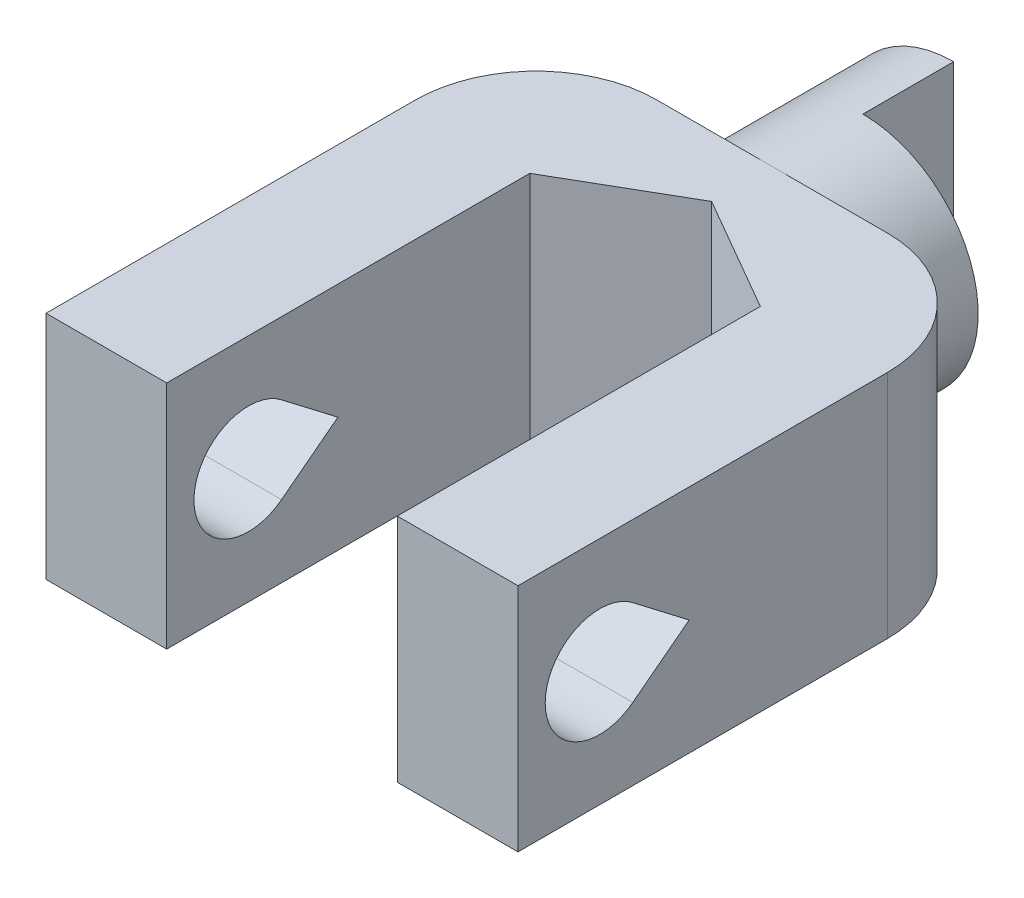
SolidWorks part; units mm, degrees
material "ABS"
ref_plane "Alzado" through (0, 0, 0) normal (0, 0, 1) x (1, 0, 0)
ref_plane "Planta" through (0, 0, 0) normal (0, 1, 0) x (1, 0, 0)
ref_plane "Vista lateral" through (0, 0, 0) normal (1, 0, 0) x (0, 0, -1)
sketch "Croquis1" plane through (0, 0, 0) normal (0, 0, 1) x (1, 0, 0)
  circle A0 centre (0, 0) radius 3.175
  dimension "D1" = 6.35
extrude "Saliente-Extruir1" add sketch "Croquis1" along normal blind 5
sketch "Croquis2" plane through (0, 0, 5) normal (0, 0, 1) x (1, 0, 0)
  line L1 (-6.5, -3.175) -> (6.5, -3.175)
  line L2 (-6.5, -3.175) -> (-6.5, 3.175)
  line L3 (-6.5, 3.175) -> (6.5, 3.175)
  line L4 (6.5, -3.175) -> (6.5, 3.175)
  line L5 (-6.5, -3.175) -> (6.5, 3.175) construction
  line L6 (-6.5, 3.175) -> (6.5, -3.175) construction
  point P0 (0, 0)
  dimension "D1" = 6.35
  dimension "D2" = 13
extrude "Saliente-Extruir2" add sketch "Croquis2" along normal blind 13.5
sketch "Croquis5" plane through (0, 0, 0) normal (0, 1, 0) x (1, 0, 0)
  line L0 (3.175, -5) -> (3.175, 0) construction
  line L1 (0, 0) -> (3.175, 0)
  line L2 (0, 0) -> (0, -2.5)
  line L3 (0, -2.5) -> (3.175, -2.5)
  line L4 (3.175, 0) -> (3.175, -2.5)
  dimension "D1" = 2.5
extrude "Cortar-Extruir2" cut sketch "Croquis5" against normal up to surface and the other way up to surface up to face at (0, 0, 5) other way up to face at (0, 0, 5)
sketch "Croquis7" plane through (0, 3.175, 0) normal (0, 1, 0) x (1, 0, 0)
  line L0 (-3.175, -18.5) -> (3.175, -18.5)
  line L1 (6.5, -18.5) -> (-6.5, -18.5) construction
  line L2 (-3.175, -18.5) -> (-3.175, -8.5)
  line L3 (-3.175, -8.5) -> (0, -6.6669)
  line L4 (0, -6.6669) -> (3.175, -8.5)
  line L5 (3.175, -8.5) -> (3.175, -18.5)
  point P5 (0, -18.5)
  dimension "D1" = 6.35
  dimension "D2" = 120
  dimension "D3" = 10
extrude "Cortar-Extruir6" cut sketch "Croquis7" against normal up to next
sketch "Croquis8" plane through (0, 3.175, 0) normal (0, 1, 0) x (1, 0, 0)
  line L0 (-6.5, -5) -> (-3.175, -5)
  line L1 (6.5, -5) -> (0, -5) construction
  line L2 (-3.175, 0) -> (-3.175, -5) construction
  line L4 (-6.5, -18.5) -> (-6.5, -5) construction
  line L5 (-6.5, -8.325) -> (-6.5, -5)
  arc A0 (-3.175, -5) -> (-6.5, -8.325) centre (-3.175, -8.325) ccw
extrude "Cortar-Extruir7" cut sketch "Croquis8" against normal up to next (6.35 mm away)
mirror "Simetría1" about plane through (0, 0, 0) normal (1, 0, 0) of "Cortar-Extruir7"
sketch "Croquis9" plane through (6.5, 0, 0) normal (1, 0, 0) x (0, 0, -1)
  line L0 (-18.5, -3.175) -> (-18.5, 3.175) construction
  line L1 (-15.3369, 1.19) -> (-13.786, 0)
  line L2 (-13.786, 0) -> (-15.3369, -1.19)
  arc A0 (-15.3369, 1.19) -> (-15.3369, -1.19) centre (-16.25, 0) ccw
  dimension "D1" = 3
  dimension "D2" = 2.25
  dimension "D3" = 75
extrude "Cortar-Extruir8" cut sketch "Croquis9" against normal up to surface (13 mm away) up to face at (-6.5, 0, 13.4125)
equation "\"D2@Croquis2\"=13"
equation "\"g\"= 6.35"
equation "\"D1@Croquis2\"=\"g\""
equation "\"d\"= 3"
equation "\"D1\"= 6.35"
equation "\"D1@Saliente-Extruir2\"=\"d\"*1.5+9"
equation "\"D1\"= \"d\" * 1.25 + 7.5"
equation "\"D1@Croquis1\"=\"g\""
equation "\"D1@Croquis7\"=\"g\""
equation "\"D3@Croquis7\"=\"d\"+7"
equation "\"D1@Croquis9\"=\"d\""
equation "\"D2@Croquis9\"=\"d\"*0.75"
